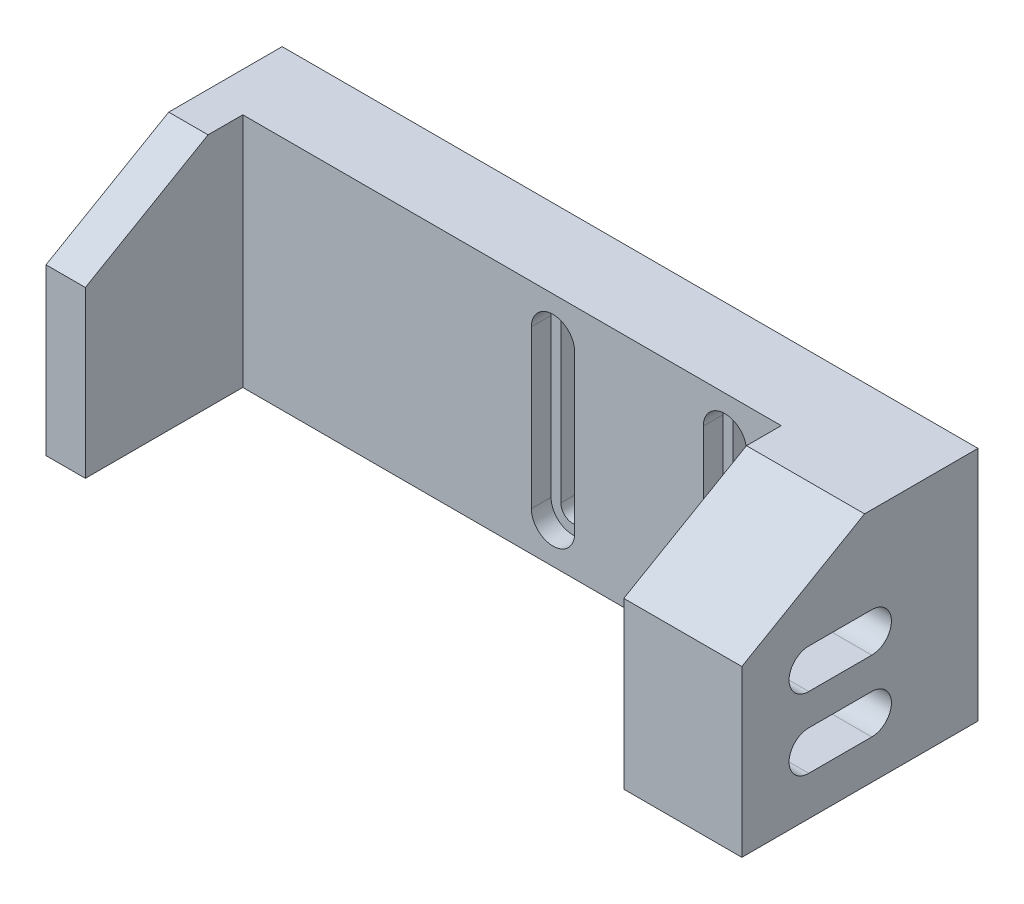
SolidWorks part; units mm, degrees
ref_plane "Front Plane" through (0, 0, 0) normal (0, 0, 1) x (1, 0, 0)
ref_plane "Top Plane" through (0, 0, 0) normal (0, 1, 0) x (1, 0, 0)
ref_plane "Right Plane" through (0, 0, 0) normal (1, 0, 0) x (0, 0, -1)
sketch "Sketch1" plane through (0, 0, 0) normal (0, 1, 0) x (1, 0, 0)
  line L0 (0, -15) -> (0, 15) construction
  line L1 (-39.2, 15) -> (39.2, 15)
  line L2 (-39.2, 15) -> (-39.2, -15)
  line L3 (-39.2, -15) -> (39.2, -15)
  line L4 (39.2, 15) -> (39.2, -15)
  line L5 (-39.2, 15) -> (39.2, -15) construction
  line L6 (-39.2, -15) -> (39.2, 15) construction
  line L7 (-34.2, 5) -> (34.2, 5)
  line L8 (-34.2, 5) -> (-34.2, -15)
  line L9 (-34.2, -15) -> (34.2, -15)
  line L10 (34.2, 5) -> (34.2, -15)
  point P0 (0, 0)
  point P10 (0, -15)
  point P11 (0, 5)
  dimension "D1" = 78.4
  dimension "D2" = 30
  dimension "D3" = 68.4
  dimension "D4" = 20
  dimension "D5" = 10
extrude "Boss-Extrude1" add sketch "Sketch1" along normal blind 30 contours L1 L10 L9 L8 L2 L3 L4
sketch "Sketch2" plane through (39.2, 0, 0) normal (1, 0, 0) x (0, 0, -1)
  line L0 (15, 0) -> (-15, 0) construction
  line L1 (-15, 30) -> (5, 30)
  line L2 (-15, 30) -> (-15, 0)
  line L3 (-15, 0) -> (5, 0)
  line L4 (5, 30) -> (5, 0)
  line L5 (5, 30) -> (-15, 30) construction
  line L6 (-15, 15) -> (5, 15) construction
  line L7 (-6.5, 7.5) -> (1.5, 7.5) construction
  line L8 (-6.5, 10) -> (1.5, 10)
  line L9 (-6.5, 5) -> (1.5, 5)
  line L10 (-6.5, 16.5) -> (1.5, 16.5) construction
  line L11 (-6.5, 19) -> (1.5, 19)
  line L12 (-6.5, 14) -> (1.5, 14)
  arc A6 (-6.5, 10) -> (-6.5, 5) centre (-6.5, 7.5) ccw
  arc A7 (1.5, 5) -> (1.5, 10) centre (1.5, 7.5) ccw
  arc A8 (-6.5, 19) -> (-6.5, 14) centre (-6.5, 16.5) ccw
  arc A9 (1.5, 14) -> (1.5, 19) centre (1.5, 16.5) ccw
  point P13 (-2.5, 16.5)
  point P18 (-2.5, 7.5)
  dimension "D1" = 2.5
  dimension "D3" = 8
  dimension "D2" = 7.5
  dimension "D4" = 7.5
  dimension "D5" = 9
extrude "Cut-Extrude1" cut sketch "Sketch2" against normal up to next
chamfer "Chamfer1" distance 9 angle 60 2 edges at (36.7, 30, 15) (-36.7, 30, 15)
sketch "Sketch8" plane through (39.2, 0, 0) normal (1, 0, 0) x (0, 0, -1)
  line L0 (15, 30) -> (0.5885, 30)
  line L1 (0.5885, 30) -> (-15, 21)
  line L2 (-15, 21) -> (-15, 0)
  line L3 (-15, 0) -> (15, 0)
  line L4 (15, 0) -> (15, 30)
  line L5 (1.5, 19) -> (1.5, 14) construction
  line L8 (-6.5, 19) -> (-6.5, 14) construction
  line L9 (-6.5, 16.5) -> (1.5, 16.5) construction
  line L10 (-6.5, 19) -> (1.5, 19)
  line L11 (-6.5, 14) -> (1.5, 14)
  line L12 (-6.5, 10) -> (-6.5, 5) construction
  line L13 (1.5, 10) -> (1.5, 5) construction
  line L14 (-6.5, 7.5) -> (1.5, 7.5) construction
  line L15 (-6.5, 10) -> (1.5, 10)
  line L16 (-6.5, 5) -> (1.5, 5)
  arc A0 (-6.5, 19) -> (-6.5, 14) centre (-6.5, 16.5) ccw
  arc A1 (1.5, 14) -> (1.5, 19) centre (1.5, 16.5) ccw
  arc A2 (-6.5, 19) -> (-6.5, 14) centre (-6.5, 16.5) ccw construction
  arc A3 (-6.5, 10) -> (-6.5, 5) centre (-6.5, 7.5) ccw
  arc A4 (1.5, 5) -> (1.5, 10) centre (1.5, 7.5) ccw
  arc A5 (-6.5, 10) -> (-6.5, 5) centre (-6.5, 7.5) ccw construction
  point P16 (-2.5, 16.5)
  point P38 (-2.5, 7.5)
extrude "Boss-Extrude8" add sketch "Sketch8" along normal blind 10
sketch "Sketch9" plane through (0, 0, -15) normal (0, 0, -1) x (-1, 0, 0)
  line L0 (-49.2, 15) -> (39.2, 15) construction
  line L5 (-49.2, 0) -> (-49.2, 30) construction
  line L6 (39.2, 30) -> (39.2, 0) construction
  line L9 (-6.71, 25) -> (-6.71, 5)
  line L10 (-28.55, 25) -> (-25.55, 25)
  line L11 (-28.55, 25) -> (-28.55, 5)
  line L12 (-28.55, 5) -> (-25.55, 5)
  line L13 (-25.55, 25) -> (-25.55, 5)
  line L14 (-28.55, 25) -> (-25.55, 5) construction
  line L15 (-28.55, 5) -> (-25.55, 25) construction
  line L16 (-6.71, 25) -> (-3.71, 25)
  line L17 (-3.71, 25) -> (-3.71, 5)
  line L18 (-6.71, 5) -> (-3.71, 5)
  circle A4 centre (-27.05, 25) radius 1.5
  circle A5 centre (-27.05, 5) radius 1.5
  circle A6 centre (-5.21, 25) radius 1.5
  circle A7 centre (-5.21, 5) radius 1.5
  point P0 (-27.05, 15)
  dimension "D2" = 3
  dimension "D1" = 22.15
  dimension "D3" = 20
extrude "Cut-Extrude2" cut sketch "Sketch9" against normal up to next contours A5 L13 A4 L11 | L10 A4 | L16 A6 | A7 L17 A6 L9 | L16 A6 | L10 A4 | L12 A5 | L12 A5 | L18 A7 | L18 A7
sketch "Sketch10" plane through (0, 0, -5) normal (0, 0, 1) x (1, 0, 0)
  line L0 (3.71, 15) -> (6.71, 15) construction
  line L7 (3.71, 5) -> (3.71, 25) construction
  line L19 (6.71, 5) -> (6.71, 25) construction
  line L29 (3.71, 25) -> (6.71, 25)
  line L30 (3.71, 25) -> (3.71, 5)
  line L31 (3.71, 5) -> (6.71, 5)
  line L32 (6.71, 25) -> (6.71, 5)
  line L33 (3.71, 25) -> (6.71, 5) construction
  line L34 (3.71, 5) -> (6.71, 25) construction
  line L35 (2.46, 26.25) -> (2.46, 3.75)
  line L36 (2.46, 3.75) -> (7.96, 3.75)
  line L37 (7.96, 26.25) -> (7.96, 3.75)
  line L38 (2.46, 26.25) -> (7.96, 26.25)
  line L39 (25.55, 25) -> (28.55, 25)
  line L40 (25.55, 25) -> (25.55, 5)
  line L41 (25.55, 5) -> (28.55, 5)
  line L42 (28.55, 25) -> (28.55, 5)
  line L43 (24.3, 26.25) -> (24.3, 3.75)
  line L44 (24.3, 3.75) -> (29.8, 3.75)
  line L45 (29.8, 26.25) -> (29.8, 3.75)
  line L46 (24.3, 26.25) -> (29.8, 26.25)
  line L47 (25.55, 15) -> (28.55, 15) construction
  line L48 (25.55, 25) -> (28.55, 5) construction
  line L49 (25.55, 5) -> (28.55, 25) construction
  circle A16 centre (5.21, 25) radius 1.5
  circle A17 centre (5.21, 5) radius 1.5
  circle A18 centre (5.21, 25) radius 2.75
  circle A19 centre (5.21, 5) radius 2.75
  circle A20 centre (27.05, 25) radius 1.5
  circle A21 centre (27.05, 5) radius 1.5
  circle A22 centre (27.05, 25) radius 2.75
  circle A23 centre (27.05, 5) radius 2.75
  point P6 (5.21, 15)
  point P26 (27.05, 15)
  line M21 (6.71, 25) -> (6.71, 5)
  line M30 (25.55, 5) -> (25.55, 25)
  line M32 (28.55, 25) -> (28.55, 5)
  arc M33 (25.55, 25) -> (28.55, 25) centre (27.05, 25) cw
  arc M34 (28.55, 5) -> (25.55, 5) centre (27.05, 5) cw
  line M35 (3.71, 5) -> (3.71, 25)
  arc M36 (3.71, 25) -> (6.71, 25) centre (5.21, 25) cw
  arc M37 (6.71, 5) -> (3.71, 5) centre (5.21, 5) cw
  dimension "D2" = 1.25
  dimension "D3" = 1.25
  dimension "D1" = 1.25
extrude "Cut-Extrude3" cut sketch "Sketch10" against normal blind 2.5 contours L38 A18 | L38 A18 L30 M36 | A18 L38 M36 M21 | A19 L37 A18 L32 | A19 L30 A18 L35 | A19 L36 M35 M37 | A19 L36 M21 M37 | L36 A19 | L46 A22 L40 M33 | A22 L46 M33 M32 | L46 A22 | A23 L40 A22 L43 | A23 L45 A22 L42 | A23 L44 M30 M34 | L44 A23 | A23 L44 M32 M34
